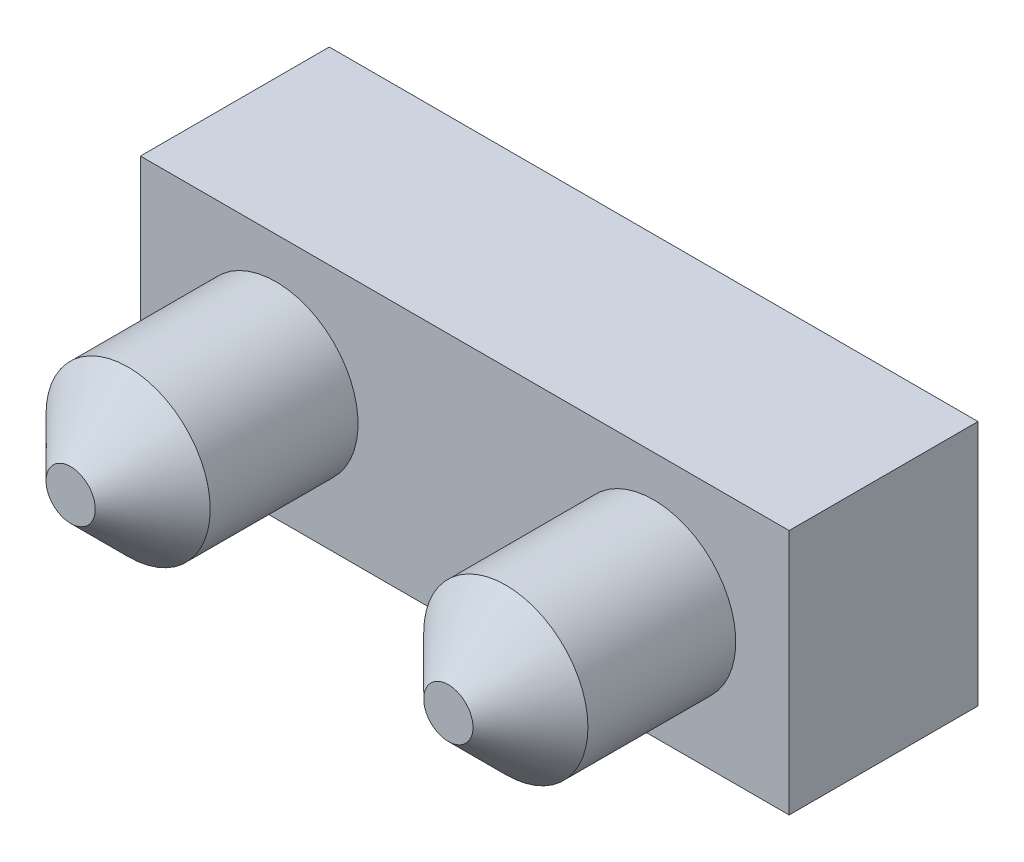
SolidWorks part; units mm, degrees
ref_plane "Přední rovina" through (0, 0, 0) normal (0, 0, 1) x (1, 0, 0)
ref_plane "Horní rovina" through (0, 0, 0) normal (0, 1, 0) x (1, 0, 0)
ref_plane "Pravá rovina" through (0, 0, 0) normal (1, 0, 0) x (0, 0, -1)
sketch "Skica1" plane through (0, 0, 0) normal (0, 0, 1) x (1, 0, 0)
  line L1 (3.95, 1.5) -> (-3.95, 1.5)
  line L2 (3.95, 1.5) -> (3.95, -1.5)
  line L3 (3.95, -1.5) -> (-3.95, -1.5)
  line L4 (-3.95, 1.5) -> (-3.95, -1.5)
  line L5 (3.95, 1.5) -> (-3.95, -1.5) construction
  line L6 (3.95, -1.5) -> (-3.95, 1.5) construction
  point P0 (0, 0)
  dimension "D1" = 3
  dimension "D2" = 7.9
extrude "Přidat vysunutím1" add sketch "Skica1" along normal blind 2.3
sketch "Skica2" plane through (0, 0, 2.3) normal (0, 0, 1) x (1, 0, 0)
  line L0 (-3.95, 1.5) -> (-3.95, -1.5) construction
  line L1 (3.95, -1.5) -> (3.95, 1.5) construction
  circle A0 centre (-2.3, 0) radius 1
  circle A1 centre (2.3, 0) radius 1
  dimension "D1" = 2
  dimension "D2" = 1.65
  dimension "D3" = 2
  dimension "D4" = 1.65
extrude "Přidat vysunutím2" add sketch "Skica2" along normal blind 2.5
chamfer "Zkosení2" distance 0.7 angle 45 2 edges at (3.3, 0, 4.8) (-1.3, 0, 4.8)
